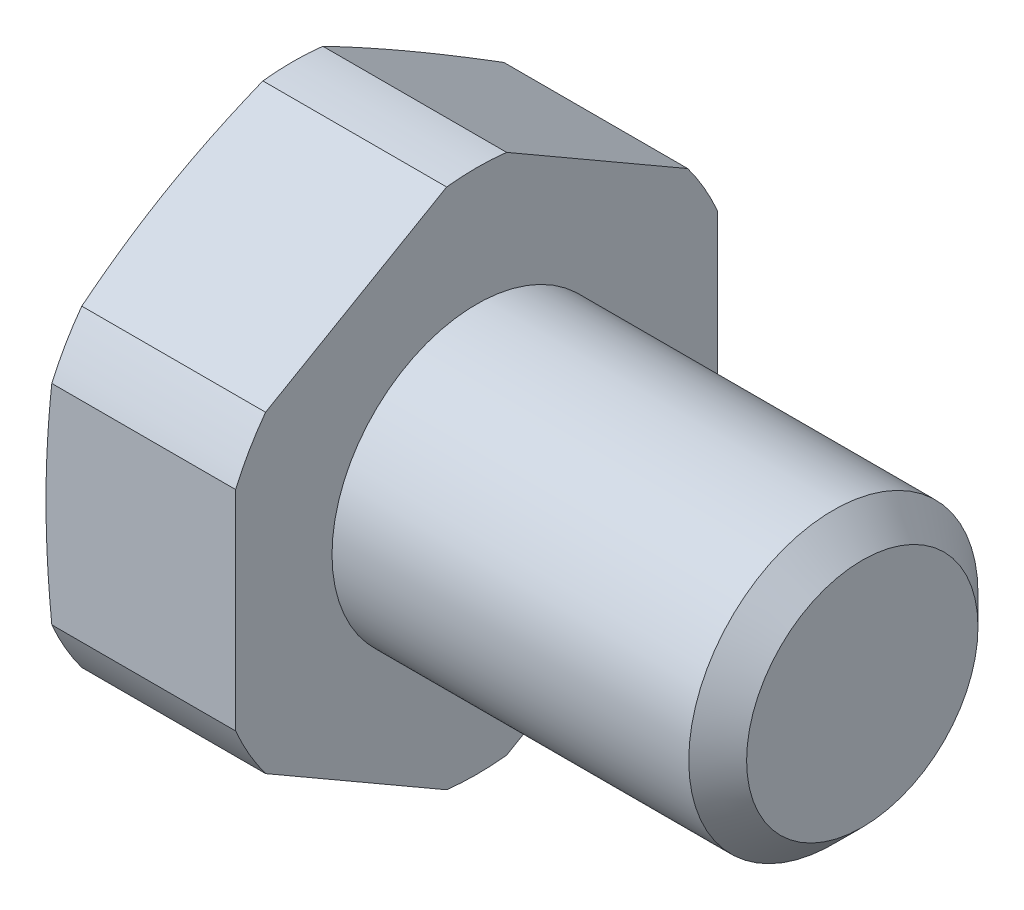
SolidWorks part; units mm, degrees
material "AISI 1020"
ref_plane "Спереди" through (0, 0, 0) normal (0, 0, 1) x (1, 0, 0)
ref_plane "Сверху" through (0, 0, 0) normal (0, 1, 0) x (1, 0, 0)
ref_plane "Справа" through (0, 0, 0) normal (1, 0, 0) x (0, 0, -1)
sketch "Эскиз1" plane through (0, 0, 0) normal (0, 0, 1) x (1, 0, 0)
  line L0 (-1000, 0) -> (49000, 0) construction
  line L1 (-4, 0) -> (-4, 4.75)
  line L2 (-4, 4.75) -> (-3.8124, 5.45)
  line L3 (-3.8124, 5.45) -> (0, 5.45)
  line L4 (0, 5.45) -> (0, 3)
  line L5 (0, 3) -> (7.4, 3)
  line L6 (8, 2.4) -> (8, 0)
  line L7 (8, 3) -> (8.5, 3.866) construction
  line L8 (8.5, 3.866) -> (9, 3) construction
  line L9 (9, 3) -> (8, 3) construction
  line L10 (8.5, 3.866) -> (8.5, 3) construction
  line L11 (8.5, 3.866) -> (0.5, 3.866) construction
  line L12 (7.4, 3) -> (8, 2.4)
  line L13 (8, 3) -> (7.7, 2.7) construction
  line L14 (-4, 4.75) -> (-14, 4.75) construction
  line L15 (-4, 0) -> (8, 0)
  dimension "l_" = 8
  dimension "b_" = 8
  dimension "_d_" = 6
  dimension "D" = 9.5
  dimension "k_" = 4
  dimension "e_" = 10.9
  dimension "shag_" = 1
  dimension "dr" = 0.866
  dimension "D1" = 0.6
  dimension "D2" = 15
  dimension "S_" = 10
revolve "Повернуть1" add sketch "Эскиз1" angle 360 about L0
cosmetic thread "Условное изображение резьбы1" parameters "D1"=8, "D2"=4.2679
sketch "Эскиз2" plane through (-4, 0, 0) normal (-1, 0, 0) x (0, 0, 1)
  line L1 (0, 5.7735) -> (-5, 2.8868)
  line L2 (-5, 2.8868) -> (-5, -2.8868)
  line L3 (-5, -2.8868) -> (0, -5.7735)
  line L4 (0, -5.7735) -> (5, -2.8868)
  line L5 (5, -2.8868) -> (5, 2.8868)
  line L6 (5, 2.8868) -> (0, 5.7735)
  circle A0 centre (0, 0) radius 5 construction
  dimension "D1" = 10
extrude "Вырез-Вытянуть1" cut sketch "Эскиз2" against normal up to surface (12 mm away) flip side to cut up to face at (8, 0, 2.4)
equation "\"D1@Эскиз1\"=\"_d_@Эскиз1\"/10"
equation "\"D@Эскиз1\"=\"S_@Эскиз1\"*0.95"
equation "\"D1@Эскиз2\"=\"S_@Эскиз1\""
equation "\"D1@Условное изображение резьбы1\"=\"b_@Эскиз1\""
equation "\"D2@Условное изображение резьбы1\"=\"_d_@Эскиз1\"-\"dr@Эскиз1\"*2"
